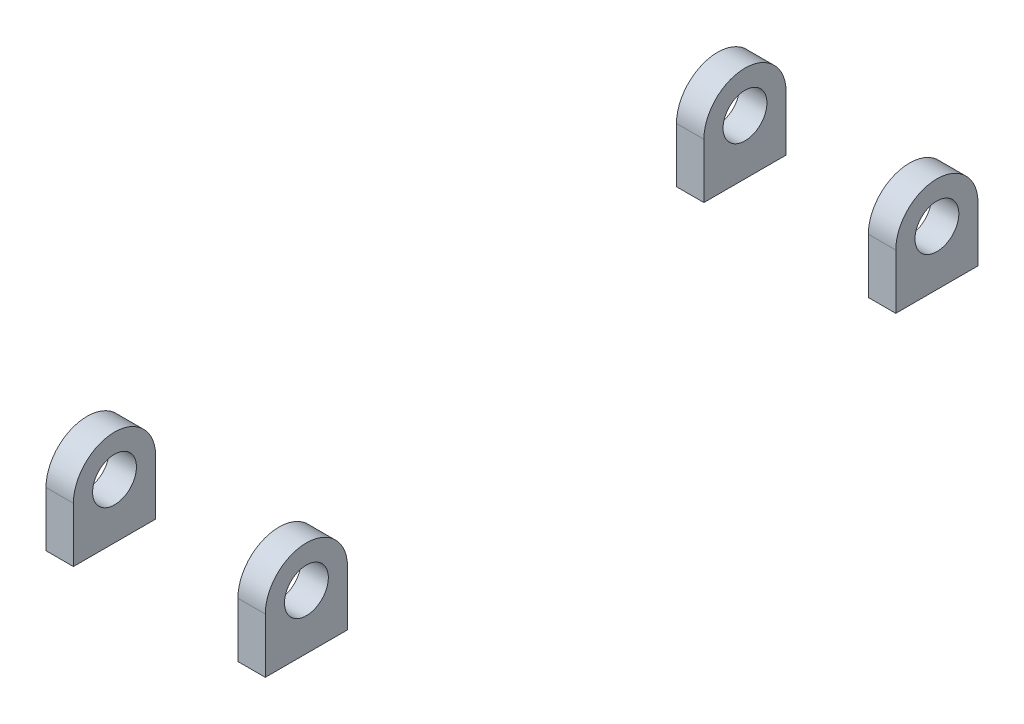
SolidWorks part; units mm, degrees
ref_plane "Front Plane" through (0, 0, 0) normal (0, 0, 1) x (1, 0, 0)
ref_plane "Top Plane" through (0, 0, 0) normal (0, 1, 0) x (1, 0, 0)
ref_plane "Right Plane" through (0, 0, 0) normal (1, 0, 0) x (0, 0, -1)
sketch "Sketch1" plane through (0, 0, 0) normal (0, 1, 0) x (1, 0, 0)
  line L0 (0, 84.6762) -> (0, -118.7938) construction
  line L6 (15, -68.8365) -> (15, -83.8365)
  line L7 (-20, -68.8365) -> (-15, -68.8365)
  line L8 (-20, 31.1635) -> (-15, 31.1635)
  line L9 (-20, 31.1635) -> (-20, 46.1635)
  line L10 (-20, 46.1635) -> (-15, 46.1635)
  line L11 (-15, 31.1635) -> (-15, 46.1635)
  line L12 (-20, -68.8365) -> (-20, -83.8365)
  line L13 (-20, -83.8365) -> (-15, -83.8365)
  line L14 (-15, -68.8365) -> (-15, -83.8365)
  line L15 (20, -83.8365) -> (15, -83.8365)
  line L16 (20, -68.8365) -> (20, -83.8365)
  line L17 (15, 31.1635) -> (15, 46.1635)
  line L18 (20, 46.1635) -> (15, 46.1635)
  line L19 (20, 31.1635) -> (20, 46.1635)
  line L20 (20, 31.1635) -> (15, 31.1635)
  line L21 (20, -68.8365) -> (15, -68.8365)
  point P0 (0, 0)
  point P20 (-20, 38.6635)
  dimension "D1" = 40
  dimension "D2" = 5
  dimension "D3" = 15
  dimension "D4" = 15
  dimension "D5" = 5
  dimension "D6" = 40
  dimension "D7" = 130
extrude "Boss-Extrude1" add sketch "Sketch1" along normal blind 20
sketch "Sketch2" plane through (-20, 0, 0) normal (-1, 0, 0) x (0, 0, 1)
  line L0 (-38.6635, 20) -> (-38.6635, 6) construction
  line L1 (-46.1635, 20) -> (-31.1635, 20) construction
  line L2 (76.3365, 20) -> (76.3365, 6) construction
  line L3 (-46.1635, 10) -> (-46.1635, 20)
  line L4 (-46.1635, 20) -> (-31.1635, 20)
  line L5 (-31.1635, 20) -> (-31.1635, 10)
  line L6 (-46.1635, 10) -> (-31.1635, 10) construction
  line L7 (68.8365, 20) -> (83.8365, 20) construction
  line L9 (68.8365, 10) -> (83.8365, 10) construction
  line L10 (68.8365, 20) -> (68.8365, 0) construction
  line L11 (83.8365, 20) -> (83.8365, 0) construction
  line L12 (68.8365, 10) -> (68.8365, 20)
  line L13 (68.8365, 20) -> (83.8365, 20)
  line L14 (83.8365, 20) -> (83.8365, 10)
  arc A0 (-31.1635, 10) -> (-46.1635, 10) centre (-38.6635, 10) ccw
  circle A1 centre (-38.6635, 10) radius 4
  arc A2 (83.8365, 10) -> (68.8365, 10) centre (76.3365, 10) ccw
  circle A3 centre (76.3365, 10) radius 4
  dimension "D1" = 8
  dimension "D2" = 10
  dimension "D3" = 8
extrude "Cut-Extrude1" cut sketch "Sketch2" against normal through all
